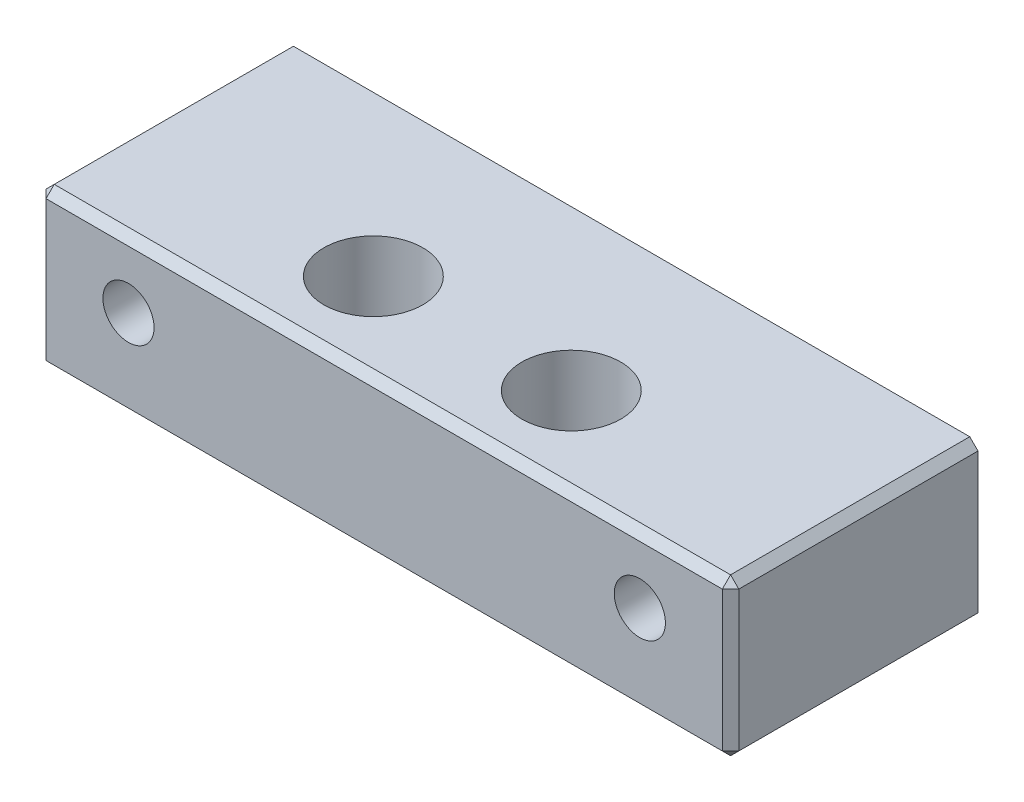
SolidWorks part; units mm, degrees
material "6061 Alloy"
ref_plane "Front Plane" through (0, 0, 0) normal (0, 0, 1) x (1, 0, 0)
ref_plane "Top Plane" through (0, 0, 0) normal (0, 1, 0) x (1, 0, 0)
ref_plane "Right Plane" through (0, 0, 0) normal (1, 0, 0) x (0, 0, -1)
sketch "Sketch1" plane through (0, 0, 0) normal (0, 0, 1) x (1, 0, 0)
  line L1 (-21, -4.75) -> (21, -4.75)
  line L2 (-21, -4.75) -> (-21, 4.75)
  line L3 (-21, 4.75) -> (21, 4.75)
  line L4 (21, -4.75) -> (21, 4.75)
  line L5 (-21, -4.75) -> (21, 4.75) construction
  line L6 (-21, 4.75) -> (21, -4.75) construction
  point P1 (0, 0)
  dimension "D1" = 42
  dimension "D2" = 9.5
extrude "Boss-Extrude1" add sketch "Sketch1" along normal mid plane 15
sketch "Sketch2" plane through (0, 0, 7.5) normal (0, 0, 1) x (1, 0, 0)
  line L0 (0, 4.5) -> (0, -4.5) construction
  line L1 (-21, 0.75) -> (21, 0.75) construction
  line L4 (21, 4.75) -> (-21, 4.75) construction
  circle A0 centre (-15.5, 0.75) radius 1.55
  circle A1 centre (15.5, 0.75) radius 1.55
  dimension "D1" = 15.5
  dimension "D3" = 3.1
  dimension "D4" = 3.1
  dimension "D2" = 15.5
  dimension "D5" = 4
extrude "Cut-Extrude1" cut sketch "Sketch2" against normal through all
sketch "Sketch4" plane through (0, 4.75, 0) normal (0, 1, 0) x (1, 0, 0)
  line L1 (0, 3.845) -> (0, -8.155) construction
  line L2 (21, 7.5) -> (-21, 7.5) construction
  circle A0 centre (6, -2.155) radius 3
  circle A1 centre (-6, -2.155) radius 3
  dimension "D1" = 6
  dimension "D4" = 6
  dimension "D2" = 6
  dimension "D3" = 9.655
  dimension "D5" = 9.655
  dimension "D6" = 6
extrude "Cut-Extrude2" cut sketch "Sketch4" against normal through all
chamfer "Chamfer3" distance 0.5 angle 45 8 edges at (21, 4.75, 0) (21, -4.75, 0) (-21, 4.75, 0) (-21, -4.75, 0) (21, 0, 7.5) (0, 4.75, 7.5) (0, -4.75, 7.5) (-21, 0, 7.5)
